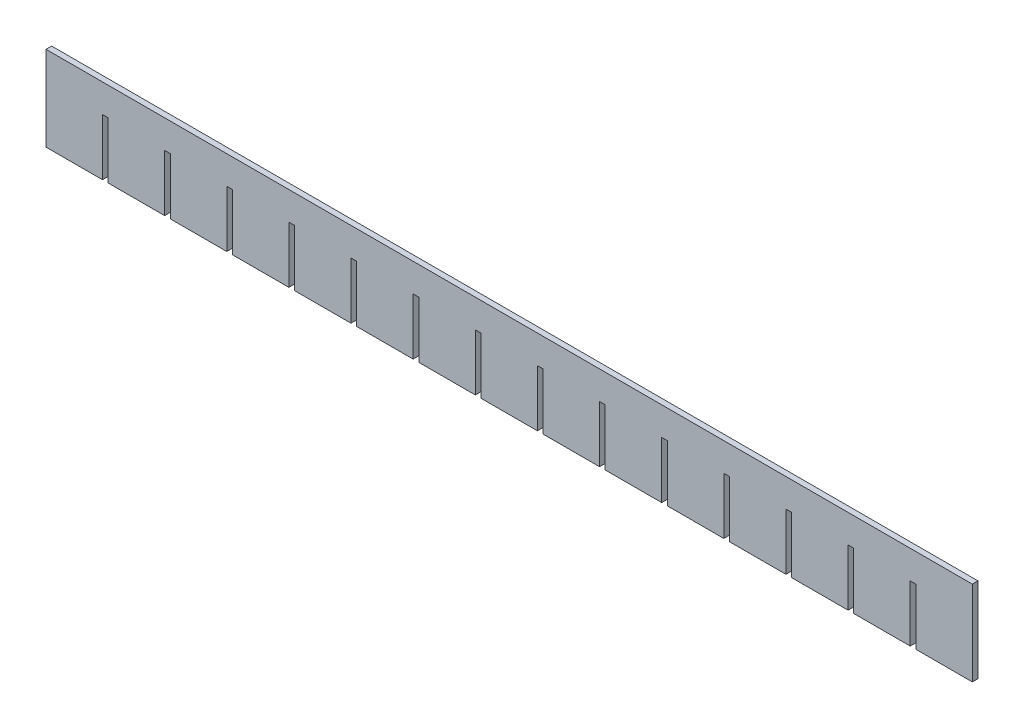
SolidWorks part; units mm, degrees
ref_plane "Ebene vorne" through (0, 0, 0) normal (0, 0, 1) x (1, 0, 0)
ref_plane "Ebene oben" through (0, 0, 0) normal (0, 1, 0) x (1, 0, 0)
ref_plane "Ebene rechts" through (0, 0, 0) normal (1, 0, 0) x (0, 0, -1)
sketch "Sketch1" plane through (0, 0, 0) normal (0, 0, 1) x (1, 0, 0)
  line L1 (-246, -22.5) -> (246, -22.5)
  line L2 (-246, -22.5) -> (-246, 22.5)
  line L3 (-246, 22.5) -> (246, 22.5)
  line L4 (246, -22.5) -> (246, 22.5)
  line L5 (-246, -22.5) -> (246, 22.5) construction
  line L6 (-246, 22.5) -> (246, -22.5) construction
  point P0 (0, 0)
  dimension "D1" = 45
  dimension "D2" = 492
extrude "Boss-Extrude1" add sketch "Sketch1" along normal blind 3
sketch "Sketch2" plane through (0, 0, 3) normal (0, 0, 1) x (1, 0, 0)
  line L6 (-246, -22.5) -> (-216, -22.5)
  line L7 (-246, -22.5) -> (246, -22.5) construction
  line L8 (-216, -22.5) -> (-216, 7.5)
  line L9 (-216, 7.5) -> (-213, 7.5)
  line L10 (-213, 7.5) -> (-213, -22.5)
  line L11 (-216, -22.5) -> (-213, -22.5)
  dimension "D1" = 30
  dimension "D2" = 30
  dimension "D3" = 3
extrude "Cut-Extrude1" cut sketch "Sketch2" against normal through all contours L11 L10 L9 L8
pattern_linear "LPattern1" count 14 spacing 33 along (1, 0, 0) of "Cut-Extrude1"
